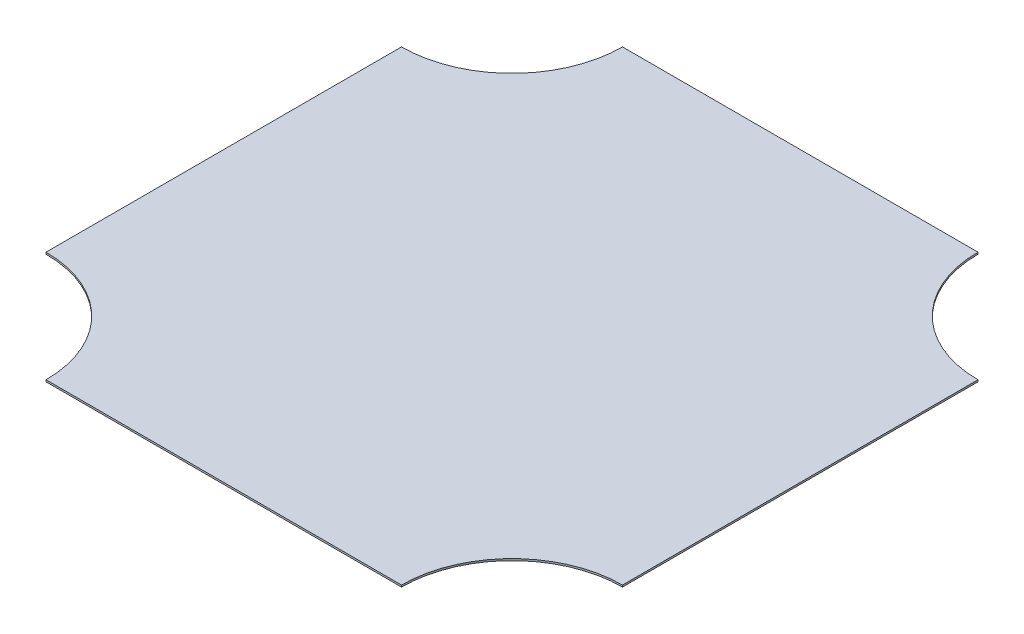
SolidWorks part; units mm, degrees
material "6061 Alloy"
ref_plane "Front Plane" through (0, 0, 0) normal (0, 0, 1) x (1, 0, 0)
ref_plane "Top Plane" through (0, 0, 0) normal (0, 1, 0) x (1, 0, 0)
ref_plane "Right Plane" through (0, 0, 0) normal (1, 0, 0) x (0, 0, -1)
sketch "Sketch1" plane through (0, 0, 0) normal (0, 1, 0) x (1, 0, 0)
  line L1 (-381, 381) -> (381, 381)
  line L2 (-381, 381) -> (-381, -381)
  line L3 (-381, -381) -> (381, -381)
  line L4 (381, 381) -> (381, -381)
  line L5 (-381, 381) -> (381, -381) construction
  line L6 (-381, -381) -> (381, 381) construction
  point P0 (0, 0)
  dimension "D1" = 762
extrude "Boss-Extrude1" add sketch "Sketch1" along normal blind 2.3813
sketch "Sketch2" plane through (0, 2.3813, 0) normal (0, 1, 0) x (1, 0, 0)
  line L0 (381, 381) -> (-381, 381) construction
  line L1 (381, -381) -> (381, 381) construction
  line L2 (234.95, 381) -> (381, 381)
  line L3 (381, 381) -> (381, 234.95)
  line L4 (381, -234.95) -> (381, -381)
  line L5 (381, -381) -> (234.95, -381)
  line L6 (-234.95, -381) -> (-381, -381)
  line L7 (-381, -381) -> (-381, -234.95)
  line L8 (-381, 234.95) -> (-381, 381)
  line L9 (-381, 381) -> (-234.95, 381)
  arc A0 (234.95, 381) -> (381, 234.95) centre (381, 381) ccw
  arc A1 (381, -234.95) -> (234.95, -381) centre (381, -381) ccw
  arc A2 (-234.95, -381) -> (-381, -234.95) centre (-381, -381) ccw
  arc A3 (-381, 234.95) -> (-234.95, 381) centre (-381, 381) ccw
  point P3 (-381, 381)
  point P21 (0, 0)
  dimension "D1" = 146.05
  dimension "D2" = 4
extrude "Cut-Extrude1" cut sketch "Sketch2" against normal through all
